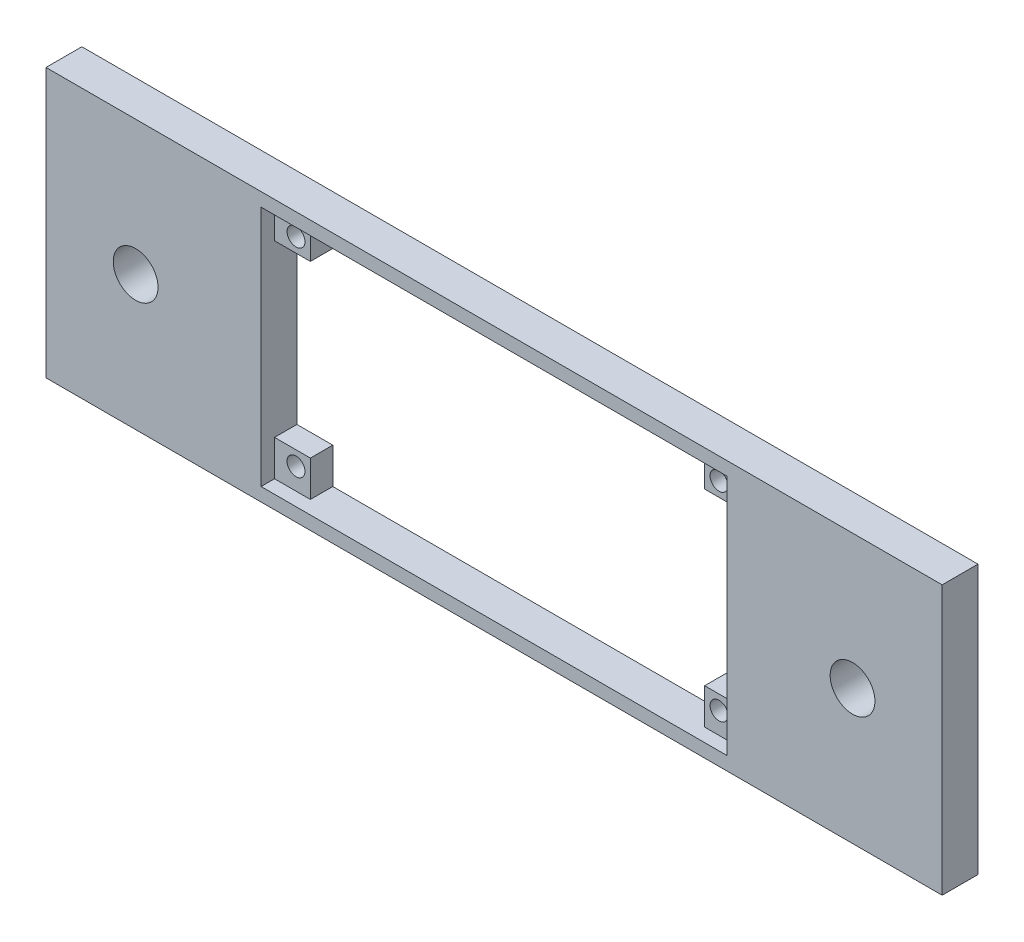
SolidWorks part; units mm, degrees
ref_plane "Front Plane" through (0, 0, 0) normal (0, 0, 1) x (1, 0, 0)
ref_plane "Top Plane" through (0, 0, 0) normal (0, 1, 0) x (1, 0, 0)
ref_plane "Right Plane" through (0, 0, 0) normal (1, 0, 0) x (0, 0, -1)
sketch "Sketch1" plane through (0, 0, 0) normal (0, 0, 1) x (1, 0, 0)
  line L0 (-50, 0) -> (50, 0) construction
  line L1 (-50, -15) -> (50, -15)
  line L2 (-50, -15) -> (-50, 15)
  line L3 (-50, 15) -> (50, 15)
  line L4 (50, -15) -> (50, 15)
  line L5 (-50, -15) -> (50, 15) construction
  line L6 (-50, 15) -> (50, -15) construction
  line L7 (-26, -13.5) -> (26, -13.5)
  line L8 (-26, -13.5) -> (-26, 13.5)
  line L9 (-26, 13.5) -> (26, 13.5)
  line L10 (26, -13.5) -> (26, 13.5)
  line L11 (-26, -13.5) -> (26, 13.5) construction
  line L12 (-26, 13.5) -> (26, -13.5) construction
  line L13 (0, 13.5) -> (0, -13.5) construction
  circle A0 centre (-40, 0) radius 2.5
  circle A1 centre (40, 0) radius 2.5
  point P0 (0, 0)
  point P6 (0, 0)
  dimension "D5" = 5
  dimension "D1" = 30
  dimension "D2" = 100
  dimension "D3" = 27
  dimension "D4" = 52
  dimension "D6" = 10
extrude "Boss-Extrude1" add sketch "Sketch1" along normal blind 4
sketch "Sketch2" plane through (0, 0, 0) normal (0, 0, 1) x (1, 0, 0)
  line L0 (0, 13.5) -> (0, -13.5) construction
  line L1 (26, 13.5) -> (-26, 13.5) construction
  line L2 (-26, -13.5) -> (26, -13.5) construction
  line L3 (-26, 0) -> (26, 0) construction
  line L4 (-26, 13.5) -> (-26, -13.5) construction
  line L5 (26, -13.5) -> (26, 13.5) construction
  line L6 (26, -9.5) -> (22, -9.5)
  line L7 (26, 13.5) -> (22, 13.5)
  line L8 (26, 13.5) -> (26, 9.5)
  line L9 (26, 9.5) -> (22, 9.5)
  line L10 (22, 13.5) -> (22, 9.5)
  line L11 (22, -13.5) -> (22, -9.5)
  line L12 (26, -13.5) -> (22, -13.5)
  line L13 (26, -13.5) -> (26, -9.5)
  line L14 (-26, -13.5) -> (-26, -9.5)
  line L15 (-26, -13.5) -> (-22, -13.5)
  line L16 (-22, -13.5) -> (-22, -9.5)
  line L17 (-26, -9.5) -> (-22, -9.5)
  line L18 (-22, 13.5) -> (-22, 9.5)
  line L19 (-26, 13.5) -> (-22, 13.5)
  line L20 (-26, 9.5) -> (-22, 9.5)
  line L21 (-26, 13.5) -> (-26, 9.5)
  circle A0 centre (23.6, 11.1) radius 1
  circle A1 centre (23.6, -11.1) radius 1
  circle A2 centre (-23.6, -11.1) radius 1
  circle A3 centre (-23.6, 11.1) radius 1
  dimension "D3" = 2
  dimension "D1" = 4
  dimension "D2" = 4
  dimension "D4" = 1.6
  dimension "D5" = 1.6
extrude "Boss-Extrude2" add sketch "Sketch2" along normal blind 2.5
